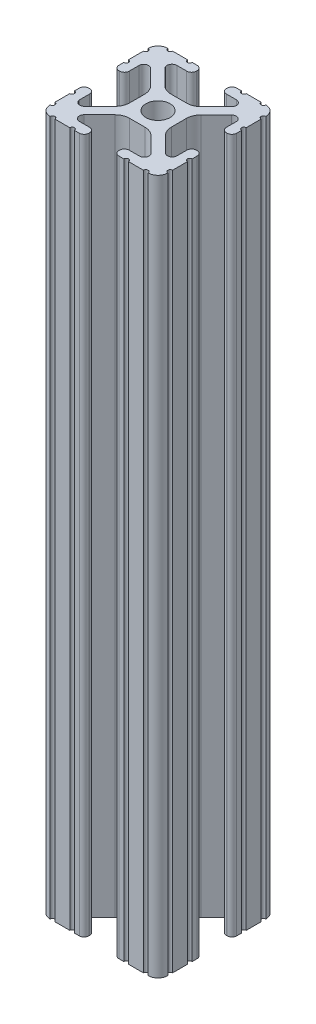
SolidWorks part; units mm, degrees
material "6061-T6 (SS)"
ref_plane "Front Plane" through (0, 0, 0) normal (0, 0, 1) x (1, 0, 0)
ref_plane "Top Plane" through (0, 0, 0) normal (0, 1, 0) x (1, 0, 0)
ref_plane "Right Plane" through (0, 0, 0) normal (1, 0, 0) x (0, 0, -1)
sketch "Sketch1" plane through (0, 0, 0) normal (0, 0, 1) x (1, 0, 0)
  line L0 (0, 0) -> (0, 150)
  dimension "D1" = 150
other "Extrusion 1010 PROFILE(1)"
ref_plane "Plane1" through (0, 0, 0) normal (0, 1, 0) x (-1, 0, 0)
sketch "Sketch11" plane through (0, 0, 0) normal (0, 1, 0) x (-1, 0, 0)
  line L1 (12.7, 12.7) -> (-12.7, 12.7) construction
  line L2 (12.7, 12.7) -> (12.7, -12.7) construction
  line L3 (12.7, -12.7) -> (-12.7, -12.7) construction
  line L4 (-12.7, 12.7) -> (-12.7, -12.7) construction
  line L5 (12.7, 12.7) -> (-12.7, -12.7) construction
  line L6 (12.7, -12.7) -> (-12.7, 12.7) construction
  line L88 (-1.7093, -4.4958) -> (1.7093, -4.4958)
  line L89 (3.9523, -5.4237) -> (7.1797, -8.6452)
  line L90 (6.4164, -10.4902) -> (4.2875, -10.4902)
  line L91 (3.2385, -11.5392) -> (3.2385, -11.651)
  line L92 (4.2875, -12.7) -> (5.3171, -12.7)
  line L93 (6.3331, -12.7) -> (9.5504, -12.7)
  line L94 (12.7, -9.5504) -> (12.7, -6.3331)
  line L95 (12.7, -5.3171) -> (12.7, -4.2875)
  line L96 (11.651, -3.2385) -> (11.5392, -3.2385)
  line L97 (10.4902, -4.2875) -> (10.4902, -6.4021)
  line L98 (8.737, -7.1292) -> (5.4405, -3.8388)
  line L99 (4.5085, -1.5917) -> (4.5085, 1.5917)
  line L100 (5.4405, 3.8388) -> (8.737, 7.1292)
  line L101 (10.4902, 6.4021) -> (10.4902, 4.2875)
  line L102 (11.5392, 3.2385) -> (11.651, 3.2385)
  line L103 (12.7, 4.2875) -> (12.7, 5.3171)
  line L104 (12.7, 6.3331) -> (12.7, 9.5504)
  line L105 (9.5504, 12.7) -> (6.3331, 12.7)
  line L106 (5.3171, 12.7) -> (4.2875, 12.7)
  line L107 (3.2384, 11.651) -> (3.2384, 11.5392)
  line L108 (4.2875, 10.4902) -> (6.4768, 10.4902)
  line L109 (7.2072, 8.7245) -> (3.9003, 5.4237)
  line L110 (1.6573, 4.4958) -> (-1.6573, 4.4958)
  line L111 (-3.9003, 5.4237) -> (-7.2072, 8.7245)
  line L112 (-6.4768, 10.4902) -> (-4.2875, 10.4902)
  line L113 (-3.2384, 11.5392) -> (-3.2384, 11.651)
  line L114 (-4.2875, 12.7) -> (-5.3171, 12.7)
  line L115 (-6.3331, 12.7) -> (-9.5504, 12.7)
  line L116 (-12.7, 9.5504) -> (-12.7, 6.3331)
  line L117 (-12.7, 5.3171) -> (-12.7, 4.2875)
  line L118 (-11.651, 3.2385) -> (-11.5392, 3.2385)
  line L119 (-10.4902, 4.2875) -> (-10.4902, 6.4021)
  line L120 (-8.737, 7.1292) -> (-5.4405, 3.8388)
  line L121 (-4.5085, 1.5917) -> (-4.5085, -1.5917)
  line L122 (-5.4405, -3.8388) -> (-8.737, -7.1292)
  line L123 (-10.4902, -6.4021) -> (-10.4902, -4.2875)
  line L124 (-11.5392, -3.2385) -> (-11.651, -3.2385)
  line L125 (-12.7, -4.2875) -> (-12.7, -5.3171)
  line L126 (-12.7, -6.3331) -> (-12.7, -9.5504)
  line L127 (-9.5504, -12.7) -> (-6.3331, -12.7)
  line L128 (-5.3171, -12.7) -> (-4.2875, -12.7)
  line L129 (-3.2385, -11.651) -> (-3.2385, -11.5392)
  line L130 (-4.2875, -10.4902) -> (-6.4164, -10.4902)
  line L131 (-7.1797, -8.6452) -> (-3.9523, -5.4237)
  circle A1 centre (0, 0) radius 2.6035
  arc A104 (-1.7093, -4.4958) -> (-3.9523, -5.4237) centre (-1.7093, -7.6708) ccw
  arc A105 (3.9523, -5.4237) -> (1.7093, -4.4958) centre (1.7093, -7.6708) ccw
  arc A106 (6.4164, -10.4902) -> (7.1797, -8.6452) centre (6.4164, -9.4098) ccw
  arc A107 (4.2875, -10.4902) -> (3.2385, -11.5392) centre (4.2875, -11.5392) ccw
  arc A108 (3.2385, -11.651) -> (4.2875, -12.7) centre (4.2875, -11.651) ccw
  arc A109 (6.3331, -12.7) -> (5.3171, -12.7) centre (5.8251, -12.7) ccw
  arc A110 (10.5664, -12.6998) -> (9.5504, -12.7) centre (10.0584, -12.7) ccw
  arc A111 (10.5664, -12.6998) -> (12.6998, -10.5664) centre (10.5918, -10.5918) ccw
  arc A112 (12.7, -9.5504) -> (12.6998, -10.5664) centre (12.7, -10.0584) ccw
  arc A113 (12.7, -5.3171) -> (12.7, -6.3331) centre (12.7, -5.8251) ccw
  arc A114 (12.7, -4.2875) -> (11.651, -3.2385) centre (11.651, -4.2875) ccw
  arc A115 (11.5392, -3.2385) -> (10.4902, -4.2875) centre (11.5392, -4.2875) ccw
  arc A116 (8.737, -7.1292) -> (10.4902, -6.4021) centre (9.4628, -6.4021) ccw
  arc A117 (4.5085, -1.5917) -> (5.4405, -3.8388) centre (7.6835, -1.5917) ccw
  arc A118 (5.4405, 3.8388) -> (4.5085, 1.5917) centre (7.6835, 1.5917) ccw
  arc A119 (10.4902, 6.4021) -> (8.737, 7.1292) centre (9.4628, 6.4021) ccw
  arc A120 (10.4902, 4.2875) -> (11.5392, 3.2385) centre (11.5392, 4.2875) ccw
  arc A121 (11.651, 3.2385) -> (12.7, 4.2875) centre (11.651, 4.2875) ccw
  arc A122 (12.7, 6.3331) -> (12.7, 5.3171) centre (12.7, 5.8251) ccw
  arc A123 (12.6998, 10.5664) -> (12.7, 9.5504) centre (12.7, 10.0584) ccw
  arc A124 (12.6998, 10.5664) -> (10.5664, 12.6998) centre (10.5918, 10.5918) ccw
  arc A125 (9.5504, 12.7) -> (10.5664, 12.6998) centre (10.0584, 12.7) ccw
  arc A126 (5.3171, 12.7) -> (6.3331, 12.7) centre (5.8251, 12.7) ccw
  arc A127 (4.2875, 12.7) -> (3.2384, 11.651) centre (4.2875, 11.651) ccw
  arc A128 (3.2384, 11.5392) -> (4.2875, 10.4902) centre (4.2875, 11.5392) ccw
  arc A129 (7.2072, 8.7245) -> (6.4768, 10.4902) centre (6.4768, 9.4563) ccw
  arc A130 (1.6573, 4.4958) -> (3.9003, 5.4237) centre (1.6573, 7.6708) ccw
  arc A131 (-3.9003, 5.4237) -> (-1.6573, 4.4958) centre (-1.6573, 7.6708) ccw
  arc A132 (-6.4768, 10.4902) -> (-7.2072, 8.7245) centre (-6.4768, 9.4563) ccw
  arc A133 (-4.2875, 10.4902) -> (-3.2384, 11.5392) centre (-4.2875, 11.5392) ccw
  arc A134 (-3.2384, 11.651) -> (-4.2875, 12.7) centre (-4.2875, 11.651) ccw
  arc A135 (-6.3331, 12.7) -> (-5.3171, 12.7) centre (-5.8251, 12.7) ccw
  arc A136 (-10.5664, 12.6998) -> (-9.5504, 12.7) centre (-10.0584, 12.7) ccw
  arc A137 (-10.5664, 12.6998) -> (-12.6998, 10.5664) centre (-10.5918, 10.5918) ccw
  arc A138 (-12.7, 9.5504) -> (-12.6998, 10.5664) centre (-12.7, 10.0584) ccw
  arc A139 (-12.7, 5.3171) -> (-12.7, 6.3331) centre (-12.7, 5.8251) ccw
  arc A140 (-12.7, 4.2875) -> (-11.651, 3.2385) centre (-11.651, 4.2875) ccw
  arc A141 (-11.5392, 3.2385) -> (-10.4902, 4.2875) centre (-11.5392, 4.2875) ccw
  arc A142 (-8.737, 7.1292) -> (-10.4902, 6.4021) centre (-9.4628, 6.4021) ccw
  arc A143 (-4.5085, 1.5917) -> (-5.4405, 3.8388) centre (-7.6835, 1.5917) ccw
  arc A144 (-5.4405, -3.8388) -> (-4.5085, -1.5917) centre (-7.6835, -1.5917) ccw
  arc A145 (-10.4902, -6.4021) -> (-8.737, -7.1292) centre (-9.4628, -6.4021) ccw
  arc A146 (-10.4902, -4.2875) -> (-11.5392, -3.2385) centre (-11.5392, -4.2875) ccw
  arc A147 (-11.651, -3.2385) -> (-12.7, -4.2875) centre (-11.651, -4.2875) ccw
  arc A148 (-12.7, -6.3331) -> (-12.7, -5.3171) centre (-12.7, -5.8251) ccw
  arc A149 (-12.6998, -10.5664) -> (-12.7, -9.5504) centre (-12.7, -10.0584) ccw
  arc A150 (-12.6998, -10.5664) -> (-10.5664, -12.6998) centre (-10.5918, -10.5918) ccw
  arc A151 (-9.5504, -12.7) -> (-10.5664, -12.6998) centre (-10.0584, -12.7) ccw
  arc A152 (-5.3171, -12.7) -> (-6.3331, -12.7) centre (-5.8251, -12.7) ccw
  arc A153 (-4.2875, -12.7) -> (-3.2385, -11.651) centre (-4.2875, -11.651) ccw
  arc A154 (-3.2385, -11.5392) -> (-4.2875, -10.4902) centre (-4.2875, -11.5392) ccw
  arc A155 (-7.1797, -8.6452) -> (-6.4164, -10.4902) centre (-6.4164, -9.4098) ccw
  point P3 (0, 0)
  point P21 (-12.7, 0)
  point P22 (0, 12.7)
  point P25 (12.7, 0)
  point P28 (0, -12.7)
  point P30 (-12.7, -12.7)
  point P33 (12.7, -12.7)
  point P37 (12.7, 12.7)
  point P40 (-12.7, 12.7)
  point P43 (0, 0)
  dimension "D1" = 25.4
ref_plane "Plane2" through (0, 0, 12.7) normal (0, 0, 1) x (1, 0, 0)
sketch "Sketch12" plane through (0, 0, 12.7) normal (0, 0, 1) x (1, 0, 0)
  line L0 (-1.6573, 150) -> (1.6573, 150) construction
  circle A0 centre (0, 137.3) radius 2.975
  circle A1 centre (0, 12.7) radius 2.975
  dimension "D2" = 5.95
  dimension "D4" = 5.95
  dimension "D1" = 12.7
  dimension "D3" = 12.7
extrude "Wrench Hole" cut sketch "Sketch12" against normal through all contours A1 | A0
ref_plane "Plane3" through (-12.7, 0, 0) normal (-1, 0, 0) x (0, 0, 1)
sketch "Sketch13" plane through (-12.7, 0, 0) normal (-1, 0, 0) x (0, 0, 1)
  line L0 (-1.5917, 150) -> (1.5917, 150) construction
  circle A0 centre (0, 137.3) radius 2.975
  circle A1 centre (0, 12.7) radius 2.975
  dimension "D2" = 5.95
  dimension "D4" = 5.95
  dimension "D1" = 12.7
  dimension "D3" = 12.7
extrude "Wrench Hole 2" cut sketch "Sketch13" against normal through all contours A0 | A1
equation "\"D2@Sketch12\"=\"wrench_hole\""
equation "\"D4@Sketch12\"=\"wrench_hole\""
equation "\"wrench_hole\"= 5.95"
equation "\"D2@Sketch13\"=\"wrench_hole\""
equation "\"D4@Sketch13\"= \"wrench_hole\""
